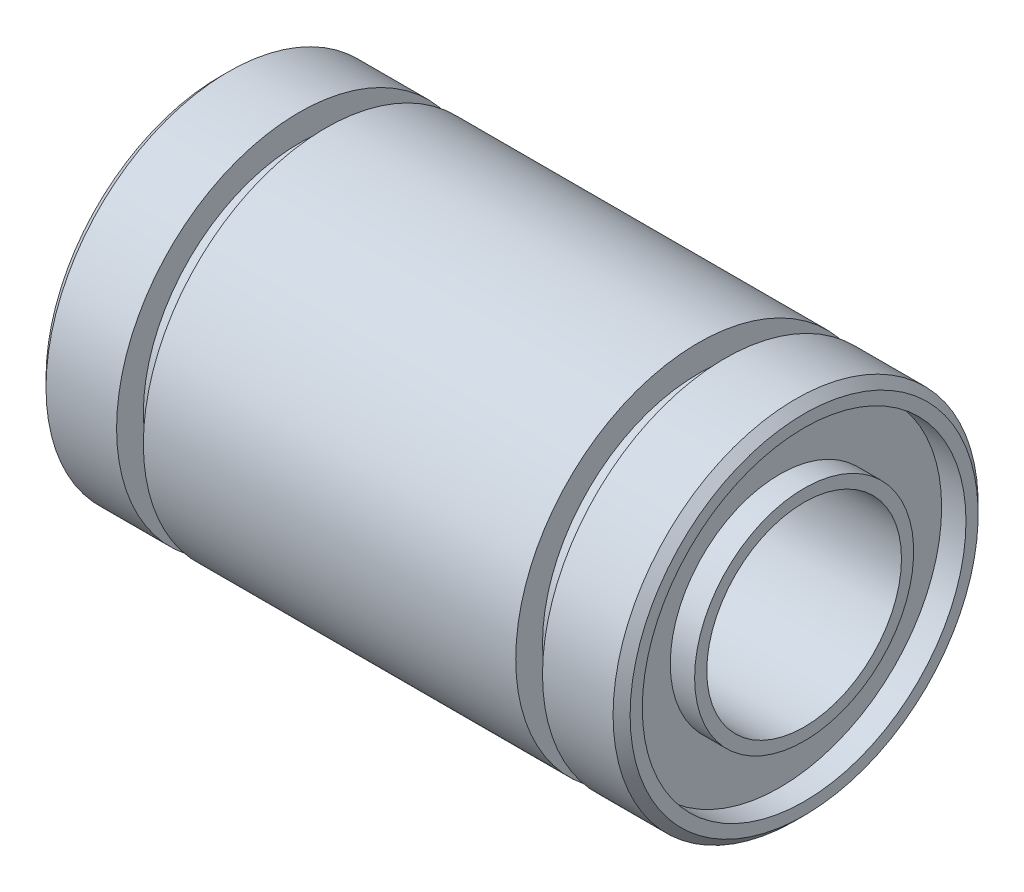
SolidWorks part; units mm, degrees
material "1060 Alloy"
ref_plane "Front Plane" through (0, 0, 0) normal (0, 0, 1) x (1, 0, 0)
ref_plane "Top Plane" through (0, 0, 0) normal (0, 1, 0) x (1, 0, 0)
ref_plane "Right Plane" through (0, 0, 0) normal (1, 0, 0) x (0, 0, -1)
sketch "Sketch1" plane through (0, 0, 0) normal (0, 0, 1) x (1, 0, 0)
  line L0 (-45.6895, 0) -> (45.6895, 0) construction
  line L1 (-11.65, 7.5) -> (-8.75, 7.5)
  line L2 (-8.75, 7.5) -> (-8.75, 6.4)
  line L3 (-8.75, 6.4) -> (-7.65, 6.4)
  line L4 (-7.65, 6.4) -> (-7.65, 7.5)
  line L5 (-7.65, 7.5) -> (7.65, 7.5)
  line L6 (0, 45.6895) -> (0, -45.6895) construction
  line L7 (-11.65, 7.5) -> (-12, 7.15)
  line L8 (-12, 7.15) -> (-12, 6.65)
  line L9 (-12, 6.65) -> (-11, 6.65)
  line L10 (-11, 6.65) -> (-11, 4.5)
  line L11 (-11, 4.5) -> (-12, 4.5)
  line L12 (-12, 4.5) -> (-12, 4)
  line L13 (-12, 4) -> (12, 4)
  line L14 (12, 4.5) -> (12, 4)
  line L15 (11, 4.5) -> (12, 4.5)
  line L16 (11, 6.65) -> (11, 4.5)
  line L17 (12, 6.65) -> (11, 6.65)
  line L18 (12, 7.15) -> (12, 6.65)
  line L19 (11.65, 7.5) -> (12, 7.15)
  line L20 (7.65, 6.4) -> (7.65, 7.5)
  line L21 (8.75, 6.4) -> (7.65, 6.4)
  line L22 (8.75, 7.5) -> (8.75, 6.4)
  line L23 (11.65, 7.5) -> (8.75, 7.5)
  point P19 (0, 4)
  point P26 (0, 7.5)
  dimension "D1" = 45
  dimension "D2" = 1.1
  dimension "L" = 24
  dimension "B" = 17.5
  dimension "W" = 1.1
  dimension "D" = 7.5
  dimension "D_1" = 7.15
  dimension "D3" = 0.5
  dimension "dr" = 4
  dimension "D4" = 0.5
  dimension "D5" = 1
revolve "Revolve1" add sketch "Sketch1" angle 360 about L0
equation "\"D\"=15"
equation "\"D1\"=14.3"
equation "\"dr\"=8"
equation "\"L\"=24"
equation "\"B\"=17.5"
equation "\"W\"=1.1"
equation "\"L@Sketch1\"= \"L\""
equation "\"B@Sketch1\"= \"B\""
equation "\"W@Sketch1\"= \"W\""
equation "\"dr@Sketch1\"= \"dr\" * 0.5"
equation "\"D@Sketch1\" = \"D\" * 0.5"
equation "\"D_1@Sketch1\" = \"D1\" * 0.5"
